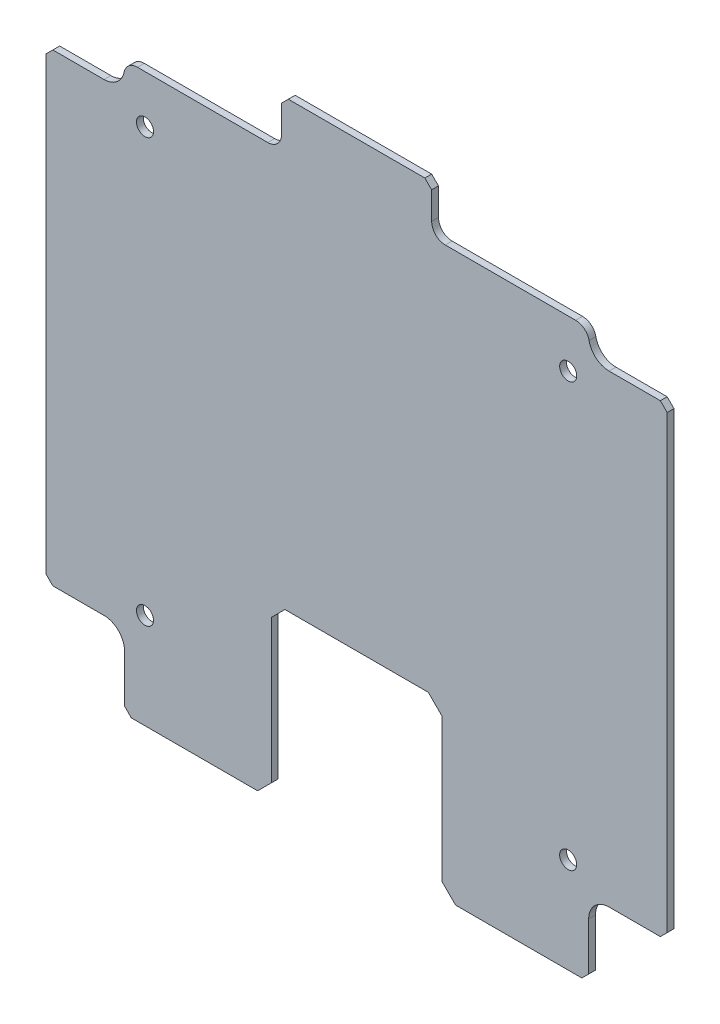
SolidWorks part; units mm, degrees
ref_plane "正面" through (0, 0, 0) normal (0, 0, 1) x (1, 0, 0)
ref_plane "平面" through (0, 0, 0) normal (0, 1, 0) x (1, 0, 0)
ref_plane "右側面" through (0, 0, 0) normal (1, 0, 0) x (0, 0, -1)
sketch "ｽｹｯﾁ1" plane through (0, 0, 0) normal (0, 0, 1) x (1, 0, 0)
  line L1 (-45.5, 45) -> (45.5, 45)
  line L2 (-45.5, 45) -> (-45.5, -45)
  line L3 (-45.5, -45) -> (45.5, -45)
  line L4 (45.5, 45) -> (45.5, -45)
  line L5 (-45.5, 34) -> (45.5, 34)
  line L6 (-45.5, 34) -> (-45.5, -34)
  line L7 (-45.5, -34) -> (45.5, -34)
  line L8 (45.5, 34) -> (45.5, -34)
  line L9 (-34, 45) -> (34, 45)
  line L10 (-34, 45) -> (-34, -45)
  line L11 (-34, -45) -> (34, -45)
  line L12 (34, 45) -> (34, -45)
  circle A0 centre (-31, 31) radius 1.25
  circle A1 centre (31, 31) radius 1.25
  circle A2 centre (31, -31) radius 1.25
  circle A3 centre (-31, -31) radius 1.25
  dimension "D15" = 2.5
  dimension "D16" = 2.5
  dimension "D17" = 2.5
  dimension "D18" = 2.5
  dimension "D1" = 90
  dimension "D2" = 91
  dimension "D3" = 45.5
  dimension "D4" = 45
  dimension "D5" = 68
  dimension "D6" = 34
  dimension "D7" = 68
  dimension "D8" = 34
  dimension "D9" = 62
  dimension "D10" = 62
  dimension "D11" = 62
  dimension "D12" = 62
  dimension "D13" = 31
  dimension "D14" = 31
extrude "ﾎﾞｽ - 押し出し2" add sketch "ｽｹｯﾁ1" along normal blind 1 contours L12 L5 L10 L7 A3 A2 A1 A0 | L12 L1 L10 L5 | L10 L5 L2 L7 | L5 L12 L7 L4 | L12 L7 L10 L3
fillet "ﾌｨﾚｯﾄ1" radius 3 4 edges at (34, -34, 0.5) (-34, -34, 0.5) (34, 34, 0.5) (-34, 34, 0.5)
sketch "ｽｹｯﾁ3" plane through (0, 0, 1) normal (0, 0, 1) x (1, 0, 0)
  line L0 (-34, -45) -> (34, -45) construction
  line L1 (-12.5, -45) -> (12.5, -45)
  line L2 (-12.5, -45) -> (-12.5, -20)
  line L3 (-12.5, -20) -> (12.5, -20)
  line L4 (12.5, -45) -> (12.5, -20)
  dimension "D1" = 25
  dimension "D2" = 25
  dimension "D3" = 12.5
extrude "ｶｯﾄ - 押し出し1" cut sketch "ｽｹｯﾁ3" against normal through all
chamfer "面取り1" distance 2 angle 45 4 edges at (12.5, -20, 0.5) (-12.5, -20, 0.5) (-12.5, -45, 0.5) (12.5, -45, 0.5)
sketch "ｽｹｯﾁ4" plane through (0, 0, 1) normal (0, 0, 1) x (1, 0, 0)
  line L0 (0, 40) -> (-40, 0)
  line L1 (-40, 0) -> (0, -40)
  line L2 (0, -40) -> (40, 0)
  line L3 (40, 0) -> (0, 40)
  circle A0 centre (0, 0) radius 40
  circle A1 centre (-20, 20) radius 1.75
  circle A2 centre (20, 20) radius 1.75
  circle A3 centre (20, -20) radius 1.75
  circle A4 centre (-20, -20) radius 1.75
  dimension "D1" = 80
  dimension "D2" = 3.5
  dimension "D3" = 3.5
  dimension "D4" = 3.5
  dimension "D5" = 3.5
sketch "ｽｹｯﾁ5" plane through (0, 0, 1) normal (0, 0, 1) x (1, 0, 0)
  line L1 (-34, 45) -> (-11, 45)
  line L2 (-34, 45) -> (-34, 38)
  line L3 (-34, 38) -> (-11, 38)
  line L4 (-11, 45) -> (-11, 38)
  line L5 (34, 45) -> (11, 45)
  line L6 (34, 45) -> (34, 38)
  line L7 (34, 38) -> (11, 38)
  line L8 (11, 45) -> (11, 38)
  dimension "D1" = 23
  dimension "D2" = 23
  dimension "D3" = 7
  dimension "D4" = 7
extrude "ｶｯﾄ - 押し出し2" cut sketch "ｽｹｯﾁ5" against normal through all
fillet "ﾌｨﾚｯﾄ2" radius 2 4 edges at (11, 38, 0.5) (34, 38, 0.5) (-11, 38, 0.5) (-34, 38, 0.5)
chamfer "面取り2" distance 1 angle 45 8 edges at (11, 45, 0.5) (-11, 45, 0.5) (-45.5, 34, 0.5) (45.5, 34, 0.5) (45.5, -34, 0.5) (34, -45, 0.5) (-45.5, -34, 0.5) (-34, -45, 0.5)
